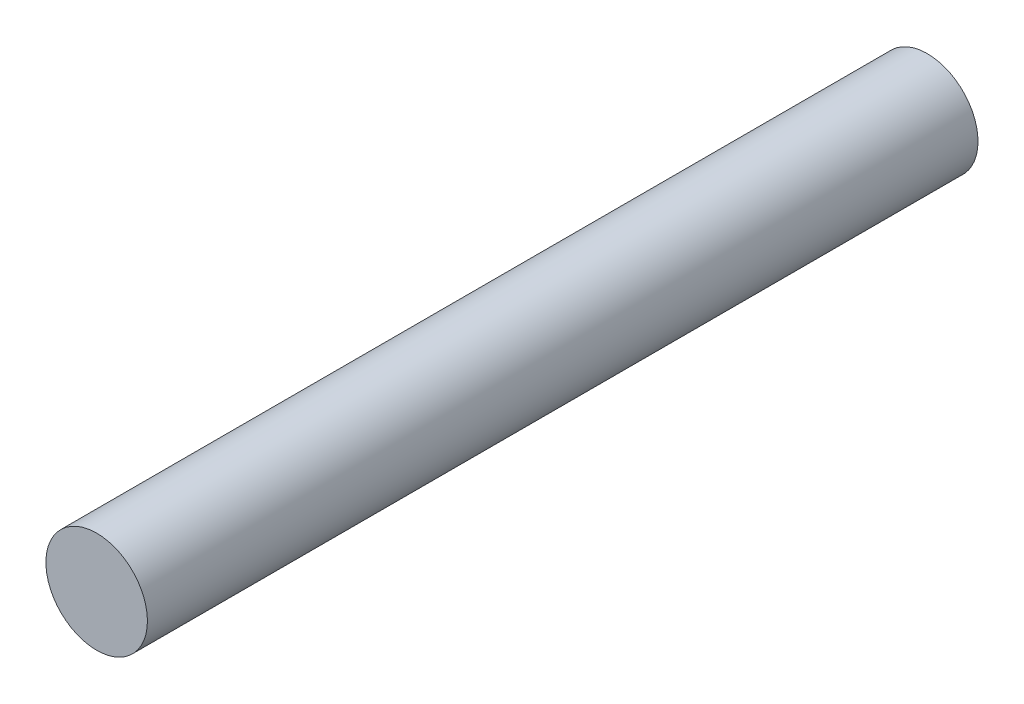
SolidWorks part; units mm, degrees
material "Tungsten"
ref_plane "Top Plane" through (0, 0, 0) normal (0, 0, 1) x (1, 0, 0)
ref_plane "Front Plane" through (0, 0, 0) normal (0, 1, 0) x (1, 0, 0)
ref_plane "Right Plane" through (0, 0, 0) normal (1, 0, 0) x (0, 0, -1)
sketch "Sketch1" plane through (0, 0, 0) normal (0, 0, 1) x (1, 0, 0)
  circle A0 centre (0, 0) radius 5.5
  dimension "D1" = 11
extrude "Boss-Extrude1" add sketch "Sketch1" along normal blind 90
